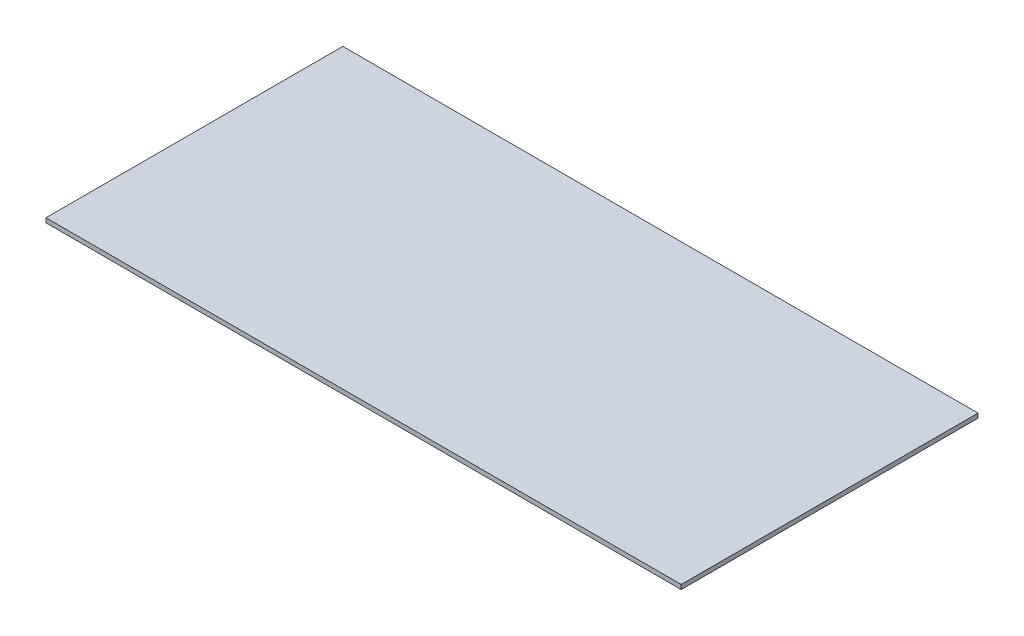
SolidWorks part; units mm, degrees
ref_plane "Plan de face" through (0, 0, 0) normal (0, 0, 1) x (1, 0, 0)
ref_plane "Plan de dessus" through (0, 0, 0) normal (0, 1, 0) x (1, 0, 0)
ref_plane "Plan de droite" through (0, 0, 0) normal (1, 0, 0) x (0, 0, -1)
sketch "Esquisse1" plane through (0, 0, 0) normal (0, 1, 0) x (1, 0, 0)
  line L1 (-214, 105) -> (214, 105)
  line L2 (-214, 105) -> (-214, -95)
  line L3 (-214, -95) -> (214, -95)
  line L4 (214, 105) -> (214, -95)
  dimension "D1" = 428
  dimension "D2" = 200
  dimension "D3" = 214
  dimension "D4" = 105
extrude "Boss.-Extru.1" add sketch "Esquisse1" along normal blind 3
